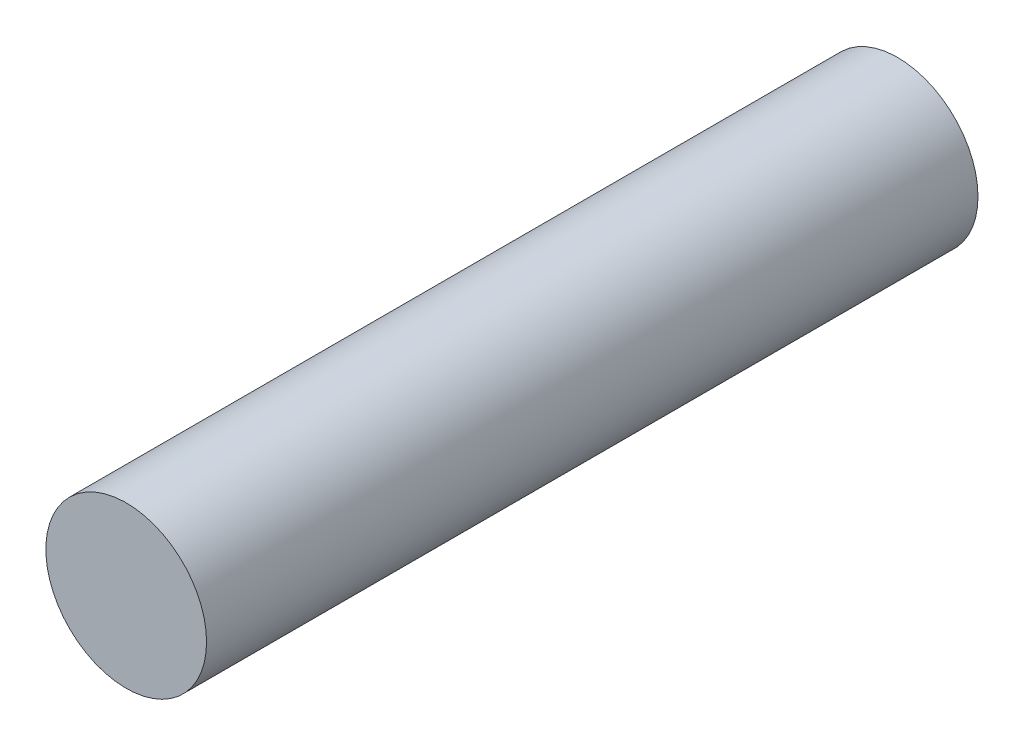
SolidWorks part; units mm, degrees
ref_plane "Front Plane" through (0, 0, 0) normal (0, 0, 1) x (1, 0, 0)
ref_plane "Top Plane" through (0, 0, 0) normal (0, 1, 0) x (1, 0, 0)
ref_plane "Right Plane" through (0, 0, 0) normal (1, 0, 0) x (0, 0, -1)
sketch "Sketch1" plane through (0, 0, 0) normal (0, 0, 1) x (1, 0, 0)
  circle A0 centre (0, 0) radius 2.5
  dimension "D1" = 5
extrude "Boss-Extrude1" add sketch "Sketch1" along normal blind 24
